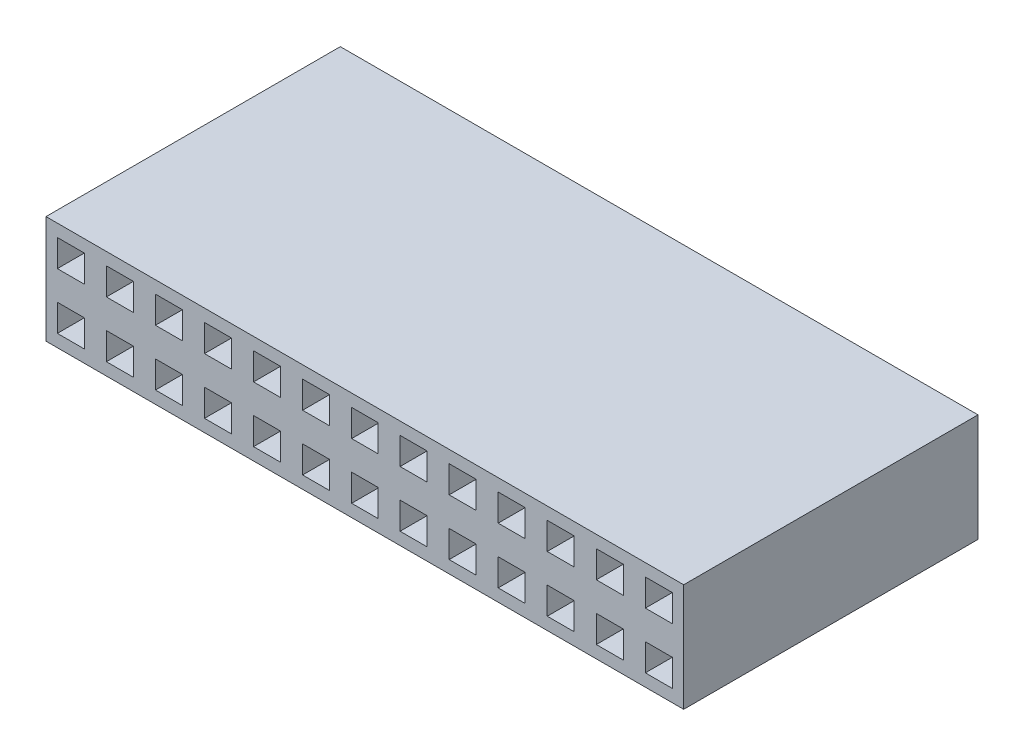
SolidWorks part; units mm, degrees
ref_plane "Front Plane" through (0, 0, 0) normal (0, 0, 1) x (1, 0, 0)
ref_plane "Top Plane" through (0, 0, 0) normal (0, 1, 0) x (1, 0, 0)
ref_plane "Right Plane" through (0, 0, 0) normal (1, 0, 0) x (0, 0, -1)
sketch "Sketch1" plane through (0, 0, 0) normal (0, 0, 1) x (1, 0, 0)
  line L0 (1.8253, -2.1501) -> (3.2223, -2.1501)
  line L1 (-16.51, -2.794) -> (16.51, -2.794)
  line L2 (-16.51, -2.794) -> (-16.51, 2.794)
  line L3 (-16.51, 2.794) -> (16.51, 2.794)
  line L4 (16.51, -2.794) -> (16.51, 2.794)
  line L5 (-16.51, -2.794) -> (16.51, 2.794) construction
  line L6 (-16.51, 2.794) -> (16.51, -2.794) construction
  line L7 (-0.6823, -2.1501) -> (0.6823, -2.1501)
  line L8 (-22.9429, 0) -> (22.3187, 0) construction
  line L9 (-0.6823, -0.7531) -> (0.6823, -0.7531)
  line L10 (0.6823, -2.1501) -> (0.6823, -0.7531)
  line L11 (-0.0162, -1.4516) -> (0.6823, -0.7531) construction
  line L12 (-0.0162, -1.4516) -> (0.6823, -2.1501) construction
  line L13 (1.8253, -2.1501) -> (1.8253, -0.7531)
  line L14 (1.8253, -0.7531) -> (3.2223, -0.7531)
  line L15 (3.2223, -2.1501) -> (3.2223, -0.7531)
  line L16 (1.8253, -2.1501) -> (3.2223, -0.7531) construction
  line L17 (1.8253, -0.7531) -> (3.2223, -2.1501) construction
  line L18 (4.3653, -2.1501) -> (5.7623, -2.1501)
  line L19 (4.3653, -2.1501) -> (4.3653, -0.7531)
  line L20 (4.3653, -0.7531) -> (5.7623, -0.7531)
  line L21 (5.7623, -2.1501) -> (5.7623, -0.7531)
  line L22 (6.9053, -2.1501) -> (8.3023, -2.1501)
  line L23 (6.9053, -2.1501) -> (6.9053, -0.7531)
  line L24 (6.9053, -0.7531) -> (8.3023, -0.7531)
  line L25 (8.3023, -2.1501) -> (8.3023, -0.7531)
  line L26 (9.4453, -2.1501) -> (10.8423, -2.1501)
  line L27 (9.4453, -2.1501) -> (9.4453, -0.7531)
  line L28 (9.4453, -0.7531) -> (10.8423, -0.7531)
  line L29 (10.8423, -2.1501) -> (10.8423, -0.7531)
  line L30 (11.9853, -2.1501) -> (13.3823, -2.1501)
  line L31 (11.9853, -2.1501) -> (11.9853, -0.7531)
  line L32 (11.9853, -0.7531) -> (13.3823, -0.7531)
  line L33 (13.3823, -2.1501) -> (13.3823, -0.7531)
  line L34 (14.5253, -2.1501) -> (15.9223, -2.1501)
  line L35 (14.5253, -2.1501) -> (14.5253, -0.7531)
  line L36 (14.5253, -0.7531) -> (15.9223, -0.7531)
  line L37 (15.9223, -2.1501) -> (15.9223, -0.7531)
  line L38 (0, 4.7463) -> (0, -4.0726) construction
  line L39 (-1.8253, -0.7531) -> (-3.2223, -2.1501) construction
  line L40 (-1.8253, -2.1501) -> (-3.2223, -0.7531) construction
  line L41 (0.0162, -1.4516) -> (-0.6823, -2.1501) construction
  line L42 (0.0162, -1.4516) -> (-0.6823, -0.7531) construction
  line L43 (-15.9223, -2.1501) -> (-15.9223, -0.7531)
  line L44 (-14.5253, -0.7531) -> (-15.9223, -0.7531)
  line L45 (-14.5253, -2.1501) -> (-14.5253, -0.7531)
  line L46 (-14.5253, -2.1501) -> (-15.9223, -2.1501)
  line L47 (-13.3823, -2.1501) -> (-13.3823, -0.7531)
  line L48 (-11.9853, -0.7531) -> (-13.3823, -0.7531)
  line L49 (-11.9853, -2.1501) -> (-11.9853, -0.7531)
  line L50 (-11.9853, -2.1501) -> (-13.3823, -2.1501)
  line L51 (-10.8423, -2.1501) -> (-10.8423, -0.7531)
  line L52 (-9.4453, -0.7531) -> (-10.8423, -0.7531)
  line L53 (-9.4453, -2.1501) -> (-9.4453, -0.7531)
  line L54 (-9.4453, -2.1501) -> (-10.8423, -2.1501)
  line L55 (-8.3023, -2.1501) -> (-8.3023, -0.7531)
  line L56 (-6.9053, -0.7531) -> (-8.3023, -0.7531)
  line L57 (-6.9053, -2.1501) -> (-6.9053, -0.7531)
  line L58 (-6.9053, -2.1501) -> (-8.3023, -2.1501)
  line L59 (-5.7623, -2.1501) -> (-5.7623, -0.7531)
  line L60 (-4.3653, -0.7531) -> (-5.7623, -0.7531)
  line L61 (-4.3653, -2.1501) -> (-4.3653, -0.7531)
  line L62 (-4.3653, -2.1501) -> (-5.7623, -2.1501)
  line L63 (-3.2223, -2.1501) -> (-3.2223, -0.7531)
  line L64 (-1.8253, -0.7531) -> (-3.2223, -0.7531)
  line L65 (-1.8253, -2.1501) -> (-1.8253, -0.7531)
  line L66 (-0.6823, -2.1501) -> (-0.6823, -0.7531)
  line L67 (-1.8253, -2.1501) -> (-3.2223, -2.1501)
  line L68 (0.0162, 1.4516) -> (-0.6823, 0.7531) construction
  line L69 (0.0162, 1.4516) -> (-0.6823, 2.1501) construction
  line L70 (-1.8253, 2.1501) -> (-3.2223, 0.7531) construction
  line L71 (-1.8253, 0.7531) -> (-3.2223, 2.1501) construction
  line L72 (1.8253, 0.7531) -> (3.2223, 2.1501) construction
  line L73 (1.8253, 2.1501) -> (3.2223, 0.7531) construction
  line L74 (-0.0162, 1.4516) -> (0.6823, 2.1501) construction
  line L75 (-0.0162, 1.4516) -> (0.6823, 0.7531) construction
  line L76 (-1.8253, 2.1501) -> (-3.2223, 2.1501)
  line L77 (-0.6823, 2.1501) -> (-0.6823, 0.7531)
  line L78 (-1.8253, 2.1501) -> (-1.8253, 0.7531)
  line L79 (-1.8253, 0.7531) -> (-3.2223, 0.7531)
  line L80 (-3.2223, 2.1501) -> (-3.2223, 0.7531)
  line L81 (-4.3653, 2.1501) -> (-5.7623, 2.1501)
  line L82 (-4.3653, 2.1501) -> (-4.3653, 0.7531)
  line L83 (-4.3653, 0.7531) -> (-5.7623, 0.7531)
  line L84 (-5.7623, 2.1501) -> (-5.7623, 0.7531)
  line L85 (-6.9053, 2.1501) -> (-8.3023, 2.1501)
  line L86 (-6.9053, 2.1501) -> (-6.9053, 0.7531)
  line L87 (-6.9053, 0.7531) -> (-8.3023, 0.7531)
  line L88 (-8.3023, 2.1501) -> (-8.3023, 0.7531)
  line L89 (-9.4453, 2.1501) -> (-10.8423, 2.1501)
  line L90 (-9.4453, 2.1501) -> (-9.4453, 0.7531)
  line L91 (-9.4453, 0.7531) -> (-10.8423, 0.7531)
  line L92 (-10.8423, 2.1501) -> (-10.8423, 0.7531)
  line L93 (-11.9853, 2.1501) -> (-13.3823, 2.1501)
  line L94 (-11.9853, 2.1501) -> (-11.9853, 0.7531)
  line L95 (-11.9853, 0.7531) -> (-13.3823, 0.7531)
  line L96 (-13.3823, 2.1501) -> (-13.3823, 0.7531)
  line L97 (-14.5253, 2.1501) -> (-15.9223, 2.1501)
  line L98 (-14.5253, 2.1501) -> (-14.5253, 0.7531)
  line L99 (-14.5253, 0.7531) -> (-15.9223, 0.7531)
  line L100 (-15.9223, 2.1501) -> (-15.9223, 0.7531)
  line L101 (15.9223, 2.1501) -> (15.9223, 0.7531)
  line L102 (14.5253, 0.7531) -> (15.9223, 0.7531)
  line L103 (14.5253, 2.1501) -> (14.5253, 0.7531)
  line L104 (14.5253, 2.1501) -> (15.9223, 2.1501)
  line L105 (13.3823, 2.1501) -> (13.3823, 0.7531)
  line L106 (11.9853, 0.7531) -> (13.3823, 0.7531)
  line L107 (11.9853, 2.1501) -> (11.9853, 0.7531)
  line L108 (11.9853, 2.1501) -> (13.3823, 2.1501)
  line L109 (10.8423, 2.1501) -> (10.8423, 0.7531)
  line L110 (9.4453, 0.7531) -> (10.8423, 0.7531)
  line L111 (9.4453, 2.1501) -> (9.4453, 0.7531)
  line L112 (9.4453, 2.1501) -> (10.8423, 2.1501)
  line L113 (8.3023, 2.1501) -> (8.3023, 0.7531)
  line L114 (6.9053, 0.7531) -> (8.3023, 0.7531)
  line L115 (6.9053, 2.1501) -> (6.9053, 0.7531)
  line L116 (6.9053, 2.1501) -> (8.3023, 2.1501)
  line L117 (5.7623, 2.1501) -> (5.7623, 0.7531)
  line L118 (4.3653, 0.7531) -> (5.7623, 0.7531)
  line L119 (4.3653, 2.1501) -> (4.3653, 0.7531)
  line L120 (4.3653, 2.1501) -> (5.7623, 2.1501)
  line L121 (3.2223, 2.1501) -> (3.2223, 0.7531)
  line L122 (1.8253, 0.7531) -> (3.2223, 0.7531)
  line L123 (1.8253, 2.1501) -> (1.8253, 0.7531)
  line L124 (0.6823, 2.1501) -> (0.6823, 0.7531)
  line L125 (-0.6823, 0.7531) -> (0.6823, 0.7531)
  line L126 (-0.6823, 2.1501) -> (0.6823, 2.1501)
  line L127 (1.8253, 2.1501) -> (3.2223, 2.1501)
  point P0 (0, 0)
  point P6 (-0.0162, -1.4516)
  point P9 (-2.5238, -1.4516)
  point P11 (2.5238, -1.4516)
  point P38 (0, -2.1501)
  point P68 (0, -0.7531)
  point P123 (0, 0.7531)
  point P124 (0, 2.1501)
  point P125 (2.5238, 1.4516)
  point P126 (-2.5238, 1.4516)
  dimension "D1" = 33.02
  dimension "D2" = 5.588
  dimension "D4" = 1.397
  dimension "D5" = 1.397
  dimension "D6" = 1.397
  dimension "D7" = 1.143
  dimension "D8" = 1.397
  dimension "D9" = 1.397
  dimension "D10" = 1.397
  dimension "D11" = 1.397
  dimension "D12" = 1.397
  dimension "D13" = 1.397
  dimension "D14" = 1.143
  dimension "D15" = 1.143
  dimension "D16" = 1.143
  dimension "D17" = 1.397
  dimension "D18" = 1.397
  dimension "D19" = 1.143
  dimension "D20" = 1.397
  dimension "D21" = 1.397
  dimension "D22" = 1.143
extrude "Boss-Extrude1" add sketch "Sketch1" along normal blind 15.24
